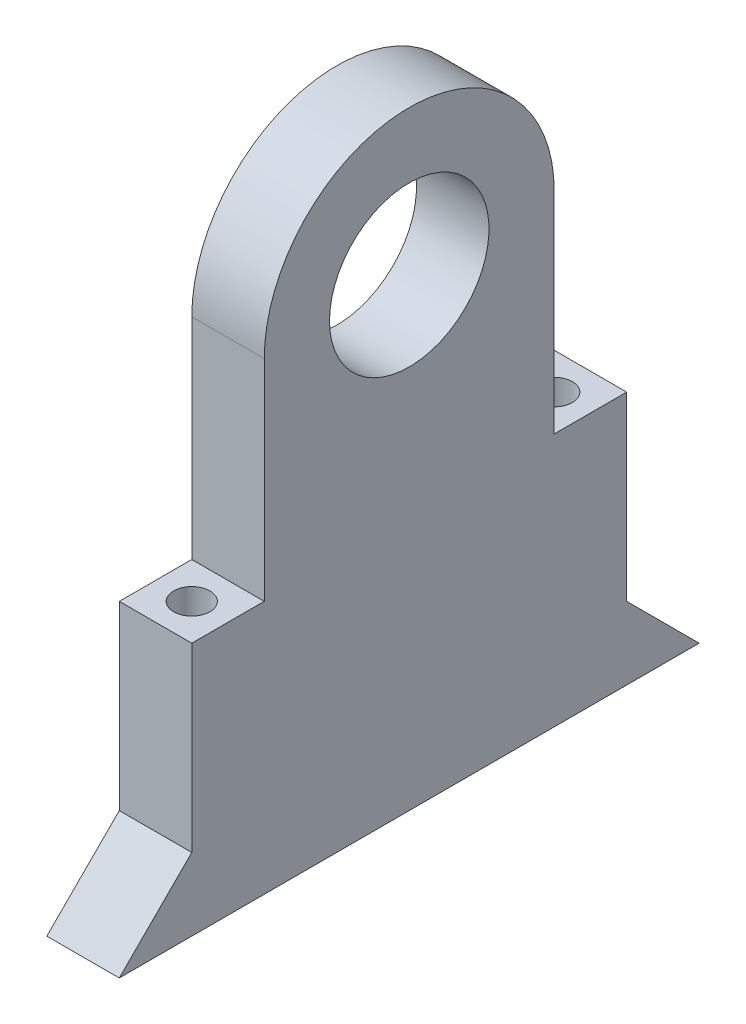
SolidWorks part; units mm, degrees
ref_plane "Front Plane" through (0, 0, 0) normal (0, 0, 1) x (1, 0, 0)
ref_plane "Top Plane" through (0, 0, 0) normal (0, 1, 0) x (1, 0, 0)
ref_plane "Right Plane" through (0, 0, 0) normal (1, 0, 0) x (0, 0, -1)
sketch "Sketch1" plane through (0, 0, 0) normal (1, 0, 0) x (0, 0, -1)
  line L0 (10, 0) -> (-10, 0)
  line L1 (-10, 17.5) -> (-10, 32)
  line L2 (0, 42) -> (0, 0) construction
  line L3 (20, 0) -> (10, 0)
  line L4 (10, 17.5) -> (10, 32)
  line L5 (15, 10) -> (15, 5)
  line L6 (-15, 5) -> (-20, 0)
  line L7 (-15, 10) -> (-15, 5)
  line L8 (-20, 0) -> (-10, 0)
  line L9 (-10, 17.5) -> (-15, 17.5)
  line L10 (15, 5) -> (20, 0)
  line L12 (15, 10) -> (15, 17.5)
  line L13 (15, 17.5) -> (10, 17.5)
  line L14 (-15, 17.5) -> (-15, 10)
  arc A0 (-10, 32) -> (10, 32) centre (0, 32) cw
  dimension "D2" = 10
  dimension "D1" = 40
  dimension "D3" = 5
  dimension "D4" = 12.5
  dimension "D5" = 5
  dimension "D6" = 10
extrude "Boss-Extrude1" add sketch "Sketch1" along normal blind 5 contours A0 L4 L13 L12 L5 L10 L3 L0 L8 L6 L7 L14 L9 L1
sketch "Sketch3" plane through (0, 0, 0) normal (-1, 0, 0) x (0, 0, 1)
  line L0 (-10, 32) -> (10, 32) construction
  line L1 (0, 32) -> (0, 0) construction
hole_wizard "Ø11.0 (11) Diameter Hole1" positions "3DSketch2" profile "Sketch4" hole size "Ø11.0" standard "ISO"
sketch3d "3DSketch2"
  point P0 (0, 32, 0)
sketch "Sketch4" plane through (0, 32, 0) normal (0, 1, 0) x (0, 0, 1)
  line L0 (0, 0) -> (0, 28.3047)
  line L1 (0, 28.3047) -> (5.5, 25)
  line L2 (5.5, 25) -> (5.5, 0)
  line L5 (5.5, 0) -> (0, 0)
  line L10 (0, 28.3047) -> (-5.5, 25) construction
  line L11 (0, -6.35) -> (0, 107.95) construction
  dimension "Hole Dia." = 11
  dimension "Hole Depth" = 25
  dimension "Drill Angle" = 118
hole_wizard "M3 Tapped Hole2" positions "Sketch10" profile "Sketch9" tap size "M3" standard "ISO"
sketch "Sketch10" plane through (0, 17.5, 0) normal (0, 1, 0) x (1, 0, 0)
  point P0 (2.5, 12.5)
sketch "Sketch9" plane through (2.5, 17.5, -12.5) normal (1, 0, 0) x (0, 0, 1)
  line L0 (0, 0) -> (0, 18.7511)
  line L1 (0, 18.7511) -> (1.25, 18)
  line L2 (1.25, 18) -> (1.25, 0)
  line L5 (1.25, 0) -> (0, 0)
  line L10 (0, 18.7511) -> (-1.25, 18) construction
  line L11 (0, -6.35) -> (0, 107.95) construction
  dimension "Tap Drill Dia." = 2.5
  dimension "Tap Drill Depth" = 18
  dimension "Drill Angle" = 118
cosmetic thread "Hole Thread4" parameters "D1"=6, "D2"=3
sketch "Sketch11" plane through (5, 0, 0) normal (1, 0, 0) x (0, 0, -1)
  line L0 (0, 0) -> (0, 14.6494) construction
  line L1 (20, 0) -> (-20, 0) construction
sketch "Sketch12" plane through (0, 0, 0) normal (0, -1, 0) x (1, 0, 0)
  line L0 (5, 0) -> (0, 0) construction
ref_plane "Plane1" through (0, 0, 0) normal (0, 0, 1) x (1, 0, 0)
mirror "Mirror1" about plane through (0, 0, 0) normal (0, 0, 1) of "M3 Tapped Hole2"
sketch "Sketch13" plane through (0, 0, 0) normal (0, -1, 0) x (1, 0, 0)
  line L0 (2.5, 0) -> (2.5, -8) construction
  line L3 (5, 0) -> (0, 0) construction
  line L4 (2.5, 0) -> (2.5, 8) construction
  dimension "D1" = 8
  dimension "D2" = 8
hole_wizard "M3 Tapped Hole3" positions "3DSketch3" profile "Sketch14" tap size "M3" standard "ISO"
sketch3d "3DSketch3"
  point P0 (2.5, 0, 8)
  point P3 (2.5, 0, 0)
  point P6 (2.5, 0, -8)
sketch "Sketch14" plane through (2.5, 0, 8) normal (1, 0, 0) x (0, 0, -1)
  line L0 (0, 0) -> (0, 8.7511)
  line L1 (0, 8.7511) -> (1.25, 8)
  line L2 (1.25, 8) -> (1.25, 0)
  line L5 (1.25, 0) -> (0, 0)
  line L10 (0, 8.7511) -> (-1.25, 8) construction
  line L11 (0, -6.35) -> (0, 107.95) construction
  dimension "Tap Drill Dia." = 2.5
  dimension "Tap Drill Depth" = 8
  dimension "Drill Angle" = 118
cosmetic thread "Hole Thread5" parameters "D1"=6, "D2"=3
cosmetic thread "Hole Thread6" parameters "D1"=6, "D2"=3
cosmetic thread "Hole Thread7" parameters "D1"=6, "D2"=3
